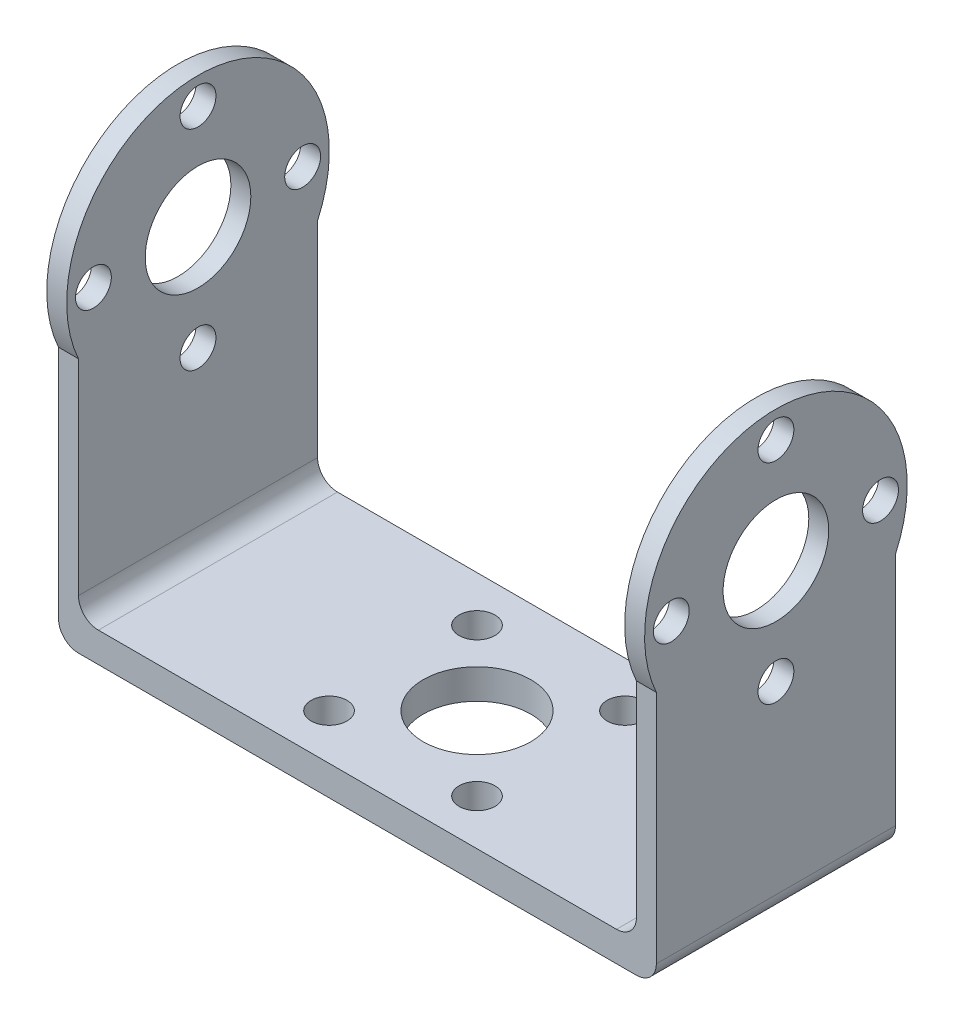
SolidWorks part; units mm, degrees
ref_plane "Alzado" through (0, 0, 0) normal (0, 0, 1) x (1, 0, 0)
ref_plane "Planta" through (0, 0, 0) normal (0, 1, 0) x (1, 0, 0)
ref_plane "Vista lateral" through (0, 0, 0) normal (1, 0, 0) x (0, 0, -1)
sketch "Croquis1" plane through (0, 0, 0) normal (0, 1, 0) x (1, 0, 0)
  line L1 (-30, 12) -> (30, 12)
  line L2 (-30, 12) -> (-30, -12)
  line L3 (-30, -12) -> (30, -12)
  line L4 (30, 12) -> (30, -12)
  line L5 (-30, 12) -> (30, -12) construction
  line L6 (-30, -12) -> (30, 12) construction
  point P0 (0, 0)
  dimension "D1" = 60
  dimension "D2" = 24
extrude "Saliente-Extruir1" add sketch "Croquis1" along normal blind 2
ref_plane "Plano1" through (30, 0, 0) normal (1, 0, 0) x (0, 0, -1)
sketch "Croquis3" plane through (30, 0, 0) normal (1, 0, 0) x (0, 0, -1)
  line L0 (-12, 2) -> (12, 2) construction
  line L1 (12, 2) -> (-12, 2)
  line L2 (12, 2) -> (12, 24.5891)
  line L3 (12, 30.04) -> (-12, 30.04) construction
  line L4 (-12, 2) -> (-12, 24.5891)
  line L5 (-12, 0) -> (12, 0) construction
  line L6 (-12, 24.5891) -> (-12, 30.04) construction
  line L7 (12, 24.5891) -> (12, 30.04) construction
  arc A0 (12, 24.5891) -> (-12, 24.5891) centre (0, 30.04) ccw
  circle A1 centre (0, 30.04) radius 5.3
  dimension "D1" = 10.6
  dimension "D3" = 26.36
  dimension "D2" = 30.04
extrude "Saliente-Extruir2" add sketch "Croquis3" against normal blind 2
sketch "Croquis5" plane through (30, 0, 0) normal (1, 0, 0) x (0, 0, -1)
  line L0 (0, 30.04) -> (0, 40.54) construction
  circle A0 centre (0, 30.04) radius 10.5 construction
  circle A1 centre (0, 40.54) radius 1.8
  circle A2 centre (10.5, 30.04) radius 1.8
  circle A3 centre (0, 19.54) radius 1.8
  circle A4 centre (-10.5, 30.04) radius 1.8
  point P14 (0, 30.04)
  dimension "D1" = 21
  dimension "D2" = 3.6
  dimension "D3" = 4
extrude "Cortar-Extruir1" cut sketch "Croquis5" against normal up to next (2 mm away)
mirror "Simetría1" about plane through (0, 0, 0) normal (1, 0, 0) of "Saliente-Extruir2", "Cortar-Extruir1"
sketch "Croquis6" plane through (0, 0, 0) normal (0, -1, 0) x (1, 0, 0)
  line L1 (-30, 12) -> (30, 12)
  line L2 (-30, 12) -> (-30, -12)
  line L3 (-30, -12) -> (30, -12)
  line L4 (30, 12) -> (30, -12)
extrude "Saliente-Extruir3" add sketch "Croquis6" along normal blind 1
sketch "Croquis7" plane through (0, -1, 0) normal (0, -1, 0) x (1, 0, 0)
  line L0 (0, 0) -> (7.4246, -7.4246) construction
  line L1 (0, 0) -> (10.5, 0) construction
  circle A0 centre (0, 0) radius 5.4
  circle A1 centre (0, 0) radius 10.5 construction
  circle A2 centre (7.4246, -7.4246) radius 1.8
  circle A3 centre (-7.4236, -7.4236) radius 1.8
  circle A4 centre (-7.4226, 7.4246) radius 1.8
  circle A5 centre (7.4256, 7.4236) radius 1.8
  point P16 (0.001, 0)
  dimension "D2" = 3.6
  dimension "D3" = 10.8
  dimension "D5" = 21
  dimension "D1" = 45
  dimension "D4" = 4
extrude "Cortar-Extruir2" cut sketch "Croquis7" against normal up to next
fillet "Redondeo1" radius 2 4 edges at (-28, 2, 0) (-30, -1, 0) (30, -1, 0)
